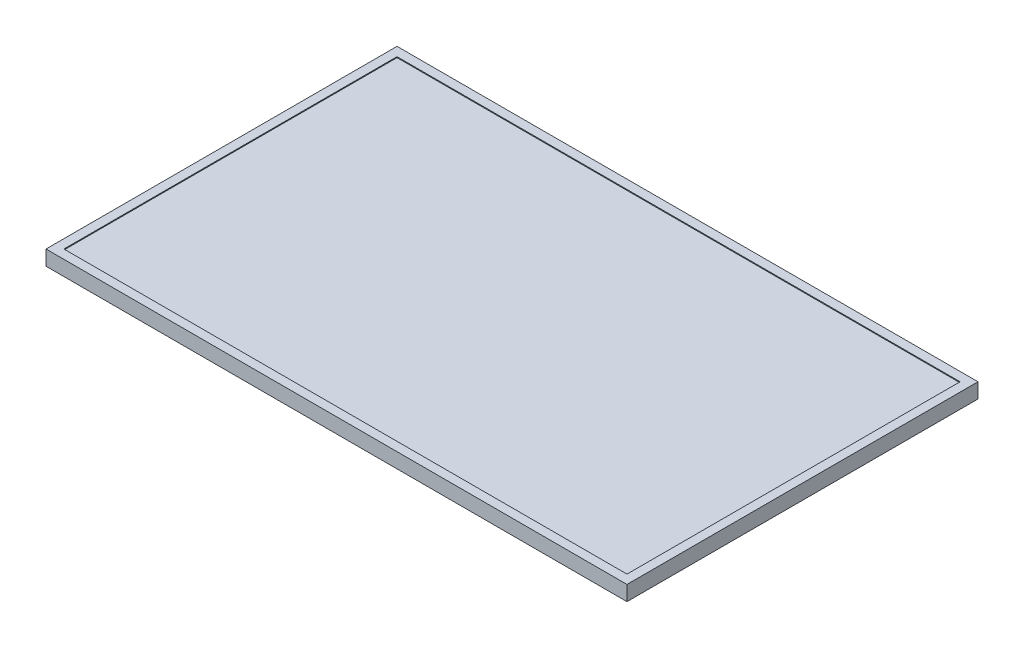
SolidWorks part; units mm, degrees
ref_plane "Front Plane" through (0, 0, 0) normal (0, 0, 1) x (1, 0, 0)
ref_plane "Top Plane" through (0, 0, 0) normal (0, 1, 0) x (1, 0, 0)
ref_plane "Right Plane" through (0, 0, 0) normal (1, 0, 0) x (0, 0, -1)
sketch "Sketch1" plane through (0, 0, 0) normal (0, 1, 0) x (1, 0, 0)
  line L1 (0, 0) -> (1649.984, 0)
  line L2 (0, 0) -> (0, 996.95)
  line L3 (0, 996.95) -> (1649.984, 996.95)
  line L4 (1649.984, 0) -> (1649.984, 996.95)
extrude "Boss-Extrude1" add sketch "Sketch1" along normal blind 39.878
sketch "Sketch2" plane through (0, 39.878, 0) normal (0, 1, 0) x (1, 0, 0)
  line L4 (25.4, 971.55) -> (25.4, 25.4)
  line L5 (25.4, 25.4) -> (1624.584, 25.4)
  line L6 (1624.584, 25.4) -> (1624.584, 971.55)
  line L7 (1624.584, 971.55) -> (25.4, 971.55)
  line L8 (0, 996.95) -> (0, 0)
  line L9 (0, 0) -> (1649.984, 0)
  line L10 (1649.984, 0) -> (1649.984, 996.95)
  line L11 (1649.984, 996.95) -> (0, 996.95)
  line L12 (0, 996.95) -> (0, 0)
  line L13 (0, 0) -> (1649.984, 0)
  line L14 (1649.984, 0) -> (1649.984, 996.95)
  line L15 (1649.984, 996.95) -> (0, 996.95)
  dimension "D1" = 0
  dimension "D2" = 25.4
extrude "Boss-Extrude2" add sketch "Sketch2" along normal blind 2.54
